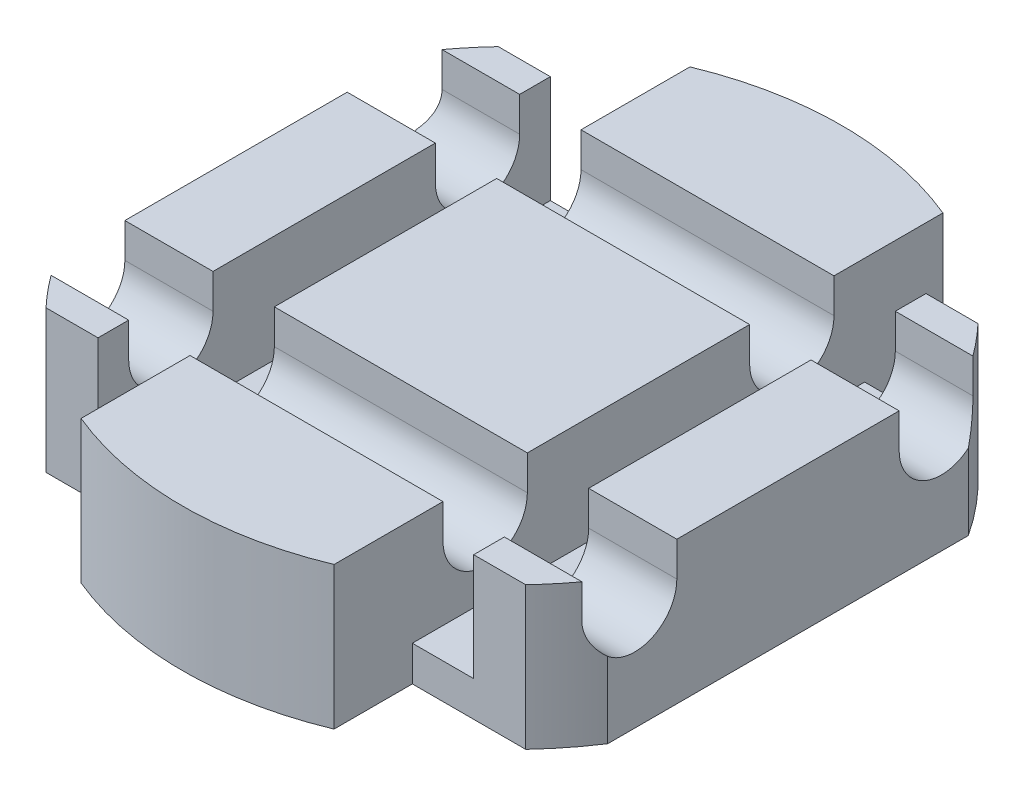
SolidWorks part; units mm, degrees
ref_plane "Ön Düzlem" through (0, 0, 0) normal (0, 0, 1) x (1, 0, 0)
ref_plane "Üst Düzlem" through (0, 0, 0) normal (0, 1, 0) x (1, 0, 0)
ref_plane "Sağ Düzlem" through (0, 0, 0) normal (1, 0, 0) x (0, 0, -1)
sketch "Çizim1" plane through (0, 0, 0) normal (0, 1, 0) x (1, 0, 0)
  line L1 (18, -11.758) -> (18, 11.758)
  line L2 (-18, -11.758) -> (-18, 11.758)
  arc A0 (-18, -11.758) -> (18, -11.758) centre (0, 0) ccw
  arc A1 (18, 11.758) -> (-18, 11.758) centre (0, 0) ccw
  dimension "D1" = 43
  dimension "D2" = 36
extrude "Yükseklik-Ekstrüzyon1" add sketch "Çizim1" against normal blind 9.3
sketch "Çizim2" plane through (0, 0, 0) normal (0, 1, 0) x (1, 0, 0)
  line L4 (8.25, -14.75) -> (15.6425, -14.75)
  line L5 (8.25, -19.8542) -> (8.25, -14.75)
  line L6 (-8.25, -19.8542) -> (-8.25, -14.75)
  line L7 (8.25, 14.75) -> (15.6425, 14.75)
  line L8 (-15.6425, -14.75) -> (-8.25, -14.75)
  line L9 (-15.6425, 14.75) -> (-8.25, 14.75)
  line L14 (8.25, 14.75) -> (8.25, 19.8542)
  line L17 (-8.25, 14.75) -> (-8.25, 19.8542)
  arc A0 (18, 11.758) -> (-18, 11.758) centre (0, 0) ccw construction
  arc A1 (-18, -11.758) -> (18, -11.758) centre (0, 0) ccw construction
  arc A2 (15.6425, 14.75) -> (8.25, 19.8542) centre (0, 0) ccw
  arc A3 (-15.6425, -14.75) -> (-8.25, -19.8542) centre (0, 0) ccw
  arc A4 (8.25, -19.8542) -> (15.6425, -14.75) centre (0, 0) ccw
  arc A5 (-8.25, 19.8542) -> (-15.6425, 14.75) centre (0, 0) ccw
extrude "Kes-Ekstrüzyon1" cut sketch "Çizim2" against normal through all
sketch "Çizim3" plane through (18, 0, 0) normal (1, 0, 0) x (0, 0, -1)
  line L0 (-11.758, 0) -> (11.758, 0) construction
  line L1 (-7.25, -2.25) -> (-7.25, 1)
  line L2 (-12.75, -2.25) -> (-12.75, 1)
  line L3 (12.75, -2.25) -> (12.75, 1)
  line L4 (7.25, -2.25) -> (7.25, 1)
  line L5 (-12.75, 1) -> (-7.25, 1)
  line L6 (7.25, 1) -> (12.75, 1)
  arc A0 (-12.75, -2.25) -> (-7.25, -2.25) centre (-10, -2.25) ccw
  arc A1 (7.25, -2.25) -> (12.75, -2.25) centre (10, -2.25) ccw
  point P4 (0, 0)
  dimension "D1" = 5.5
  dimension "D2" = 20
  dimension "D3" = 10
  dimension "D4" = 5
  dimension "D5" = 1
extrude "Kes-Ekstrüzyon2" cut sketch "Çizim3" against normal through all
sketch "Çizim4" plane through (0, 0, 0) normal (0, 0, 1) x (1, 0, 0)
  line L1 (-12.25, -7) -> (-8.25, -7)
  line L2 (-12.25, -7) -> (-12.25, 0)
  line L3 (-12.25, 0) -> (-8.25, 0)
  line L4 (-8.25, -7) -> (-8.25, 0)
  line L5 (-12.25, -7) -> (-8.25, 0) construction
  line L6 (-12.25, 0) -> (-8.25, -7) construction
  line L7 (8.25, -7) -> (12.25, -7)
  line L8 (8.25, -7) -> (8.25, 0)
  line L9 (8.25, 0) -> (12.25, 0)
  line L10 (12.25, -7) -> (12.25, 0)
  line L11 (8.25, -7) -> (12.25, 0) construction
  line L12 (8.25, 0) -> (12.25, -7) construction
  line L14 (15.6425, 0) -> (8.25, 0) construction
  line L15 (-8.25, -9.3) -> (-8.25, 0) construction
  line L16 (8.25, -9.3) -> (8.25, 0) construction
  point P0 (-10.25, -3.5)
  point P5 (10.25, -3.5)
  dimension "D1" = 7
  dimension "D2" = 4
extrude "Kes-Ekstrüzyon3" cut sketch "Çizim4" against normal mid plane 50
